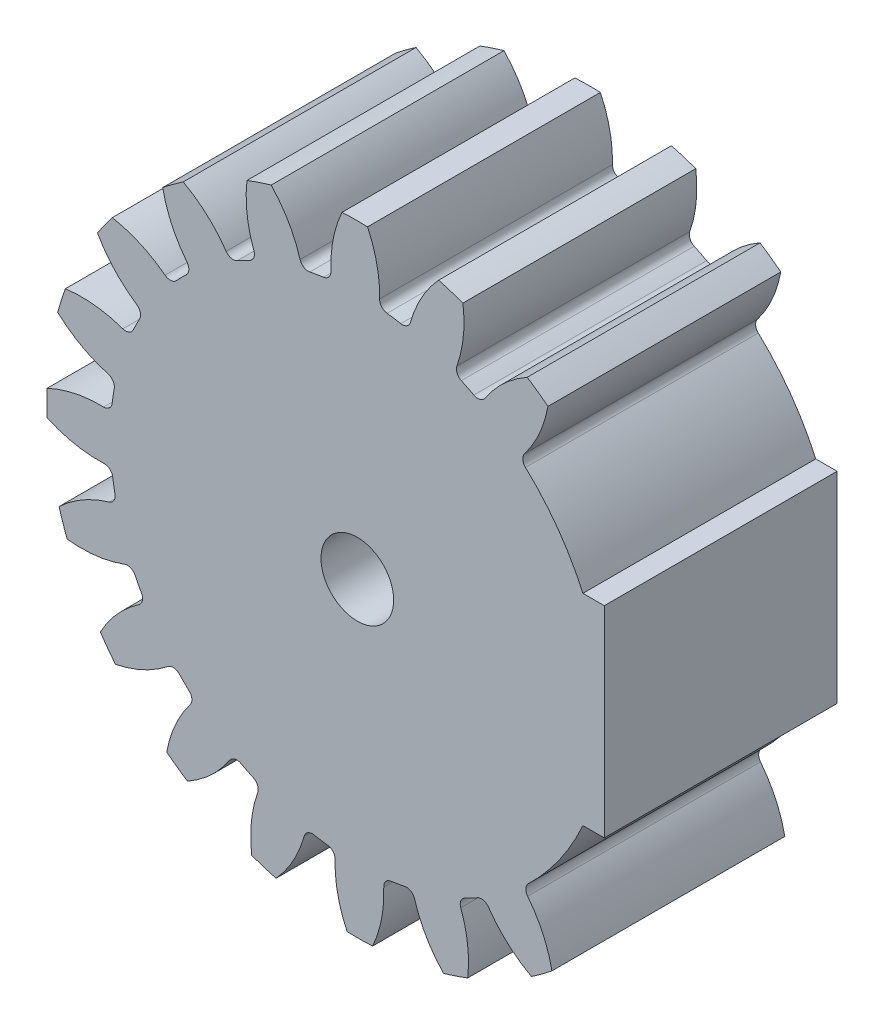
SolidWorks part; units mm, degrees
material "1023 Carbon Steel Sheet (SS)"
ref_plane "Front Plane" through (0, 0, 0) normal (0, 0, 1) x (1, 0, 0)
ref_plane "Top Plane" through (0, 0, 0) normal (0, 1, 0) x (1, 0, 0)
ref_plane "Right Plane" through (0, 0, 0) normal (1, 0, 0) x (0, 0, -1)
sketch "skBase" plane through (0, 0, 0) normal (0, 0, 1) x (1, 0, 0)
  circle A0 centre (0, 0) radius 20
  circle A1 centre (0, 0) radius 22
  circle A2 centre (0, 0) radius 17.5
  dimension "D1" = 40
  dimension "D3" = 4.5
extrude "Base" add sketch "skBase" along normal mid plane 16.5 contours A1
sketch "skToothProfile" plane through (0, 0, 0) normal (0, 0, 1) x (1, 0, 0)
  line L0 (0, 0) -> (0, 22) construction
  line L1 (-1.5692, 19.9383) -> (1.5692, 19.9383) construction
  line L2 (-1.0563, 17.4681) -> (0, 0) construction
  line L3 (0, 15.6271) -> (-2.6287, 22.8493) construction
  line L4 (0, 0) -> (3.4416, 21.7291) construction
  line L5 (1.5692, 19.9383) -> (4.6689, 19.4474) construction
  circle A0 centre (0, 0) radius 22 construction
  arc A1 (-1.0563, 17.4681) -> (-3.258, 22.7681) centre (-9.8105, 16.9387) ccw
  arc A2 (1.0563, 17.4681) -> (3.258, 22.7681) centre (9.8105, 16.9387) cw
  circle A3 centre (0, 0) radius 17.5 construction
  arc A4 (1.0563, 17.4681) -> (-1.0563, 17.4681) centre (0, 0) ccw
  circle A5 centre (0, 0) radius 20 construction
  circle A6 centre (0, 0) radius 22 construction
  circle A7 centre (0, 0) radius 23
  arc A8 (3.258, 22.7681) -> (-3.258, 22.7681) centre (0, 0) ccw
  dimension "D2" = 20
  dimension "D3" = 9
  dimension "D1" = 1
extrude "ToothProfile" cut sketch "skToothProfile" against normal through all and the other way through all
fillet "FilletToothProfile" radius 0.6 2 edges at (1.0563, 17.4681, 0) (-1.0563, 17.4681, 0)
pattern_circular "CirPatternTeeth" count 20 over 360 about axis through (0, 0, 0) along (0, 0, 1) of "ToothProfile", "FilletToothProfile"
sketch "skChaveta" plane through (0, 0, 8.25) normal (0, 0, 1) x (1, 0, 0)
  line L0 (0, 2.575) -> (0, 0) construction
  circle A0 centre (0, 0) radius 2.575
  dimension "D1" = 5.15
extrude "Chaveta" cut sketch "skChaveta" against normal through all
sketch "skRebaixo" plane through (0, 0, 8.25) normal (0, 0, 1) x (1, 0, 0)
  circle A0 centre (0, 0) radius 21.5
  circle A1 centre (0, 0) radius 7.5
  dimension "D1" = 43
  dimension "D2" = 15
sketch "Sketch4" plane through (0, 0, -8.25) normal (0, 0, -1) x (-1, 0, 0)
  circle A0 centre (0, 0) radius 17.5
  arc A5 (-2.5459, 21.8522) -> (-4.3314, 21.5694) centre (0, 0) ccw
  arc A6 (-2.5459, 21.8522) -> (-4.3314, 21.5694) centre (0, 0) ccw
  arc A7 (-18.0189, -1.107) -> (-21.8522, -2.5459) centre (-16.9387, -9.8105) ccw
  arc A8 (-18.0189, -1.107) -> (-21.8522, -2.5459) centre (-16.9387, -9.8105) ccw
  arc A9 (-21.5694, -4.3314) -> (-17.4791, -4.5153) centre (-19.1413, 4.096) ccw
  arc A10 (-21.5694, -4.3314) -> (-17.4791, -4.5153) centre (-19.1413, 4.096) ccw
  arc A127 (-19.996, -9.174) -> (-19.1752, -10.7848) centre (0, 0) ccw
  arc A128 (-19.996, -9.174) -> (-19.1752, -10.7848) centre (0, 0) ccw
  arc A129 (-16.1824, -14.904) -> (-14.904, -16.1824) centre (0, 0) ccw
  arc A130 (-16.1824, -14.904) -> (-14.904, -16.1824) centre (0, 0) ccw
  arc A131 (-10.7848, -19.1752) -> (-9.174, -19.996) centre (0, 0) ccw
  arc A132 (-10.7848, -19.1752) -> (-9.174, -19.996) centre (0, 0) ccw
  arc A133 (-4.3314, -21.5694) -> (-2.5459, -21.8522) centre (0, 0) ccw
  arc A134 (-4.3314, -21.5694) -> (-2.5459, -21.8522) centre (0, 0) ccw
  arc A135 (2.5459, -21.8522) -> (4.3314, -21.5694) centre (0, 0) ccw
  arc A136 (2.5459, -21.8522) -> (4.3314, -21.5694) centre (0, 0) ccw
  arc A137 (9.174, -19.996) -> (10.7848, -19.1752) centre (0, 0) ccw
  arc A138 (9.174, -19.996) -> (10.7848, -19.1752) centre (0, 0) ccw
  arc A139 (14.904, -16.1824) -> (16.1824, -14.904) centre (0, 0) ccw
  arc A140 (14.904, -16.1824) -> (16.1824, -14.904) centre (0, 0) ccw
  arc A141 (19.1752, -10.7848) -> (19.996, -9.174) centre (0, 0) ccw
  arc A142 (19.1752, -10.7848) -> (19.996, -9.174) centre (0, 0) ccw
  arc A143 (21.5694, -4.3314) -> (21.8522, -2.5459) centre (0, 0) ccw
  arc A144 (21.5694, -4.3314) -> (21.8522, -2.5459) centre (0, 0) ccw
  arc A145 (21.8522, 2.5459) -> (21.5694, 4.3314) centre (0, 0) ccw
  arc A146 (21.8522, 2.5459) -> (21.5694, 4.3314) centre (0, 0) ccw
  arc A147 (19.996, 9.174) -> (19.1752, 10.7848) centre (0, 0) ccw
  arc A148 (19.996, 9.174) -> (19.1752, 10.7848) centre (0, 0) ccw
  arc A149 (16.1824, 14.904) -> (14.904, 16.1824) centre (0, 0) ccw
  arc A150 (16.1824, 14.904) -> (14.904, 16.1824) centre (0, 0) ccw
  arc A151 (10.7848, 19.1752) -> (9.174, 19.996) centre (0, 0) ccw
  arc A152 (10.7848, 19.1752) -> (9.174, 19.996) centre (0, 0) ccw
  arc A153 (4.3314, 21.5694) -> (2.5459, 21.8522) centre (0, 0) ccw
  arc A154 (4.3314, 21.5694) -> (2.5459, 21.8522) centre (0, 0) ccw
  arc A155 (-9.174, 19.996) -> (-10.7848, 19.1752) centre (0, 0) ccw
  arc A156 (-9.174, 19.996) -> (-10.7848, 19.1752) centre (0, 0) ccw
  arc A157 (-14.904, 16.1824) -> (-16.1824, 14.904) centre (0, 0) ccw
  arc A158 (-14.904, 16.1824) -> (-16.1824, 14.904) centre (0, 0) ccw
  arc A159 (-19.1752, 10.7848) -> (-19.996, 9.174) centre (0, 0) ccw
  arc A160 (-19.1752, 10.7848) -> (-19.996, 9.174) centre (0, 0) ccw
  arc A161 (-21.5694, 4.3314) -> (-21.8522, 2.5459) centre (0, 0) ccw
  arc A162 (-21.5694, 4.3314) -> (-21.8522, 2.5459) centre (0, 0) ccw
  arc A163 (-4.3314, 21.5694) -> (-4.5153, 17.4791) centre (4.096, 19.1413) ccw
  arc A164 (-4.3314, 21.5694) -> (-4.5153, 17.4791) centre (4.096, 19.1413) ccw
  arc A165 (-4.9352, 16.7897) -> (-4.5153, 17.4791) centre (-5.1044, 17.3653) ccw
  arc A166 (-4.9352, 16.7897) -> (-4.5153, 17.4791) centre (-5.1044, 17.3653) ccw
  arc A167 (-4.9352, 16.7897) -> (-5.8761, 16.484) centre (0, 0) ccw
  arc A168 (-4.9352, 16.7897) -> (-5.8761, 16.484) centre (0, 0) ccw
  arc A169 (-6.621, 16.7949) -> (-5.8761, 16.484) centre (-6.0775, 17.0492) ccw
  arc A170 (-6.621, 16.7949) -> (-5.8761, 16.484) centre (-6.0775, 17.0492) ccw
  arc A171 (-6.621, 16.7949) -> (-9.174, 19.996) centre (-14.5647, 13.0781) ccw
  arc A172 (-6.621, 16.7949) -> (-9.174, 19.996) centre (-14.5647, 13.0781) ccw
  arc A173 (-10.7848, 19.1752) -> (-9.6956, 15.2283) centre (-2.0195, 19.4702) ccw
  arc A174 (-10.7848, 19.1752) -> (-9.6956, 15.2283) centre (-2.0195, 19.4702) ccw
  arc A175 (-9.882, 14.4429) -> (-9.6956, 15.2283) centre (-10.2208, 14.9381) ccw
  arc A176 (-9.882, 14.4429) -> (-9.6956, 15.2283) centre (-10.2208, 14.9381) ccw
  arc A177 (-9.882, 14.4429) -> (-10.6823, 13.8614) centre (0, 0) ccw
  arc A178 (-9.882, 14.4429) -> (-10.6823, 13.8614) centre (0, 0) ccw
  arc A179 (-11.4868, 13.9269) -> (-10.6823, 13.8614) centre (-11.0486, 14.3366) ccw
  arc A180 (-11.4868, 13.9269) -> (-10.6823, 13.8614) centre (-11.0486, 14.3366) ccw
  arc A181 (-11.4868, 13.9269) -> (-14.904, 16.1824) centre (-17.8932, 7.9372) ccw
  arc A182 (-11.4868, 13.9269) -> (-14.904, 16.1824) centre (-17.8932, 7.9372) ccw
  arc A183 (-16.1824, 14.904) -> (-13.9269, 11.4868) centre (-7.9372, 17.8932) ccw
  arc A184 (-16.1824, 14.904) -> (-13.9269, 11.4868) centre (-7.9372, 17.8932) ccw
  arc A185 (-13.8614, 10.6823) -> (-13.9269, 11.4868) centre (-14.3366, 11.0486) ccw
  arc A186 (-13.8614, 10.6823) -> (-13.9269, 11.4868) centre (-14.3366, 11.0486) ccw
  arc A187 (-13.8614, 10.6823) -> (-14.4429, 9.882) centre (0, 0) ccw
  arc A188 (-13.8614, 10.6823) -> (-14.4429, 9.882) centre (0, 0) ccw
  arc A189 (-15.2283, 9.6956) -> (-14.4429, 9.882) centre (-14.9381, 10.2208) ccw
  arc A190 (-15.2283, 9.6956) -> (-14.4429, 9.882) centre (-14.9381, 10.2208) ccw
  arc A191 (-15.2283, 9.6956) -> (-19.1752, 10.7848) centre (-19.4702, 2.0195) ccw
  arc A192 (-15.2283, 9.6956) -> (-19.1752, 10.7848) centre (-19.4702, 2.0195) ccw
  arc A193 (-19.996, 9.174) -> (-16.7949, 6.621) centre (-13.0781, 14.5647) ccw
  arc A194 (-19.996, 9.174) -> (-16.7949, 6.621) centre (-13.0781, 14.5647) ccw
  arc A195 (-16.484, 5.8761) -> (-16.7949, 6.621) centre (-17.0492, 6.0775) ccw
  arc A196 (-16.484, 5.8761) -> (-16.7949, 6.621) centre (-17.0492, 6.0775) ccw
  arc A197 (-16.484, 5.8761) -> (-16.7897, 4.9352) centre (0, 0) ccw
  arc A198 (-16.484, 5.8761) -> (-16.7897, 4.9352) centre (0, 0) ccw
  arc A199 (-17.4791, 4.5153) -> (-16.7897, 4.9352) centre (-17.3653, 5.1044) ccw
  arc A200 (-17.4791, 4.5153) -> (-16.7897, 4.9352) centre (-17.3653, 5.1044) ccw
  arc A201 (-17.4791, 4.5153) -> (-21.5694, 4.3314) centre (-19.1413, -4.096) ccw
  arc A202 (-17.4791, 4.5153) -> (-21.5694, 4.3314) centre (-19.1413, -4.096) ccw
  arc A203 (-21.8522, 2.5459) -> (-18.0189, 1.107) centre (-16.9387, 9.8105) ccw
  arc A204 (-21.8522, 2.5459) -> (-18.0189, 1.107) centre (-16.9387, 9.8105) ccw
  arc A205 (-17.493, 0.4946) -> (-18.0189, 1.107) centre (-18.0928, 0.5116) ccw
  arc A206 (-17.493, 0.4946) -> (-18.0189, 1.107) centre (-18.0928, 0.5116) ccw
  arc A207 (-17.493, 0.4946) -> (-17.493, -0.4946) centre (0, 0) ccw
  arc A208 (-17.493, 0.4946) -> (-17.493, -0.4946) centre (0, 0) ccw
  arc A209 (-18.0189, -1.107) -> (-17.493, -0.4946) centre (-18.0928, -0.5116) ccw
  arc A210 (-18.0189, -1.107) -> (-17.493, -0.4946) centre (-18.0928, -0.5116) ccw
  arc A211 (-16.7897, -4.9352) -> (-17.4791, -4.5153) centre (-17.3653, -5.1044) ccw
  arc A212 (-16.7897, -4.9352) -> (-17.4791, -4.5153) centre (-17.3653, -5.1044) ccw
  arc A213 (-16.7897, -4.9352) -> (-16.484, -5.8761) centre (0, 0) ccw
  arc A214 (-16.7897, -4.9352) -> (-16.484, -5.8761) centre (0, 0) ccw
  arc A215 (-16.7949, -6.621) -> (-16.484, -5.8761) centre (-17.0492, -6.0775) ccw
  arc A216 (-16.7949, -6.621) -> (-16.484, -5.8761) centre (-17.0492, -6.0775) ccw
  arc A217 (-16.7949, -6.621) -> (-19.996, -9.174) centre (-13.0781, -14.5647) ccw
  arc A218 (-16.7949, -6.621) -> (-19.996, -9.174) centre (-13.0781, -14.5647) ccw
  arc A219 (-19.1752, -10.7848) -> (-15.2283, -9.6956) centre (-19.4702, -2.0195) ccw
  arc A220 (-19.1752, -10.7848) -> (-15.2283, -9.6956) centre (-19.4702, -2.0195) ccw
  arc A221 (-14.4429, -9.882) -> (-15.2283, -9.6956) centre (-14.9381, -10.2208) ccw
  arc A222 (-14.4429, -9.882) -> (-15.2283, -9.6956) centre (-14.9381, -10.2208) ccw
  arc A223 (-14.4429, -9.882) -> (-13.8614, -10.6823) centre (0, 0) ccw
  arc A224 (-14.4429, -9.882) -> (-13.8614, -10.6823) centre (0, 0) ccw
  arc A225 (-13.9269, -11.4868) -> (-13.8614, -10.6823) centre (-14.3366, -11.0486) ccw
  arc A226 (-13.9269, -11.4868) -> (-13.8614, -10.6823) centre (-14.3366, -11.0486) ccw
  arc A227 (-13.9269, -11.4868) -> (-16.1824, -14.904) centre (-7.9372, -17.8932) ccw
  arc A228 (-13.9269, -11.4868) -> (-16.1824, -14.904) centre (-7.9372, -17.8932) ccw
  arc A229 (-14.904, -16.1824) -> (-11.4868, -13.9269) centre (-17.8932, -7.9372) ccw
  arc A230 (-14.904, -16.1824) -> (-11.4868, -13.9269) centre (-17.8932, -7.9372) ccw
  arc A231 (-10.6823, -13.8614) -> (-11.4868, -13.9269) centre (-11.0486, -14.3366) ccw
  arc A232 (-10.6823, -13.8614) -> (-11.4868, -13.9269) centre (-11.0486, -14.3366) ccw
  arc A233 (-10.6823, -13.8614) -> (-9.882, -14.4429) centre (0, 0) ccw
  arc A234 (-10.6823, -13.8614) -> (-9.882, -14.4429) centre (0, 0) ccw
  arc A235 (-9.6956, -15.2283) -> (-9.882, -14.4429) centre (-10.2208, -14.9381) ccw
  arc A236 (-9.6956, -15.2283) -> (-9.882, -14.4429) centre (-10.2208, -14.9381) ccw
  arc A237 (-9.6956, -15.2283) -> (-10.7848, -19.1752) centre (-2.0195, -19.4702) ccw
  arc A238 (-9.6956, -15.2283) -> (-10.7848, -19.1752) centre (-2.0195, -19.4702) ccw
  arc A239 (-9.174, -19.996) -> (-6.621, -16.7949) centre (-14.5647, -13.0781) ccw
  arc A240 (-9.174, -19.996) -> (-6.621, -16.7949) centre (-14.5647, -13.0781) ccw
  arc A241 (-5.8761, -16.484) -> (-6.621, -16.7949) centre (-6.0775, -17.0492) ccw
  arc A242 (-5.8761, -16.484) -> (-6.621, -16.7949) centre (-6.0775, -17.0492) ccw
  arc A243 (-5.8761, -16.484) -> (-4.9352, -16.7897) centre (0, 0) ccw
  arc A244 (-5.8761, -16.484) -> (-4.9352, -16.7897) centre (0, 0) ccw
  arc A245 (-4.5153, -17.4791) -> (-4.9352, -16.7897) centre (-5.1044, -17.3653) ccw
  arc A246 (-4.5153, -17.4791) -> (-4.9352, -16.7897) centre (-5.1044, -17.3653) ccw
  arc A247 (-4.5153, -17.4791) -> (-4.3314, -21.5694) centre (4.096, -19.1413) ccw
  arc A248 (-4.5153, -17.4791) -> (-4.3314, -21.5694) centre (4.096, -19.1413) ccw
  arc A249 (-2.5459, -21.8522) -> (-1.107, -18.0189) centre (-9.8105, -16.9387) ccw
  arc A250 (-2.5459, -21.8522) -> (-1.107, -18.0189) centre (-9.8105, -16.9387) ccw
  arc A251 (-0.4946, -17.493) -> (-1.107, -18.0189) centre (-0.5116, -18.0928) ccw
  arc A252 (-0.4946, -17.493) -> (-1.107, -18.0189) centre (-0.5116, -18.0928) ccw
  arc A253 (-0.4946, -17.493) -> (0.4946, -17.493) centre (0, 0) ccw
  arc A254 (-0.4946, -17.493) -> (0.4946, -17.493) centre (0, 0) ccw
  arc A255 (1.107, -18.0189) -> (0.4946, -17.493) centre (0.5116, -18.0928) ccw
  arc A256 (1.107, -18.0189) -> (0.4946, -17.493) centre (0.5116, -18.0928) ccw
  arc A257 (1.107, -18.0189) -> (2.5459, -21.8522) centre (9.8105, -16.9387) ccw
  arc A258 (1.107, -18.0189) -> (2.5459, -21.8522) centre (9.8105, -16.9387) ccw
  arc A259 (4.3314, -21.5694) -> (4.5153, -17.4791) centre (-4.096, -19.1413) ccw
  arc A260 (4.3314, -21.5694) -> (4.5153, -17.4791) centre (-4.096, -19.1413) ccw
  arc A261 (4.9352, -16.7897) -> (4.5153, -17.4791) centre (5.1044, -17.3653) ccw
  arc A262 (4.9352, -16.7897) -> (4.5153, -17.4791) centre (5.1044, -17.3653) ccw
  arc A263 (4.9352, -16.7897) -> (5.8761, -16.484) centre (0, 0) ccw
  arc A264 (4.9352, -16.7897) -> (5.8761, -16.484) centre (0, 0) ccw
  arc A265 (6.621, -16.7949) -> (5.8761, -16.484) centre (6.0775, -17.0492) ccw
  arc A266 (6.621, -16.7949) -> (5.8761, -16.484) centre (6.0775, -17.0492) ccw
  arc A267 (6.621, -16.7949) -> (9.174, -19.996) centre (14.5647, -13.0781) ccw
  arc A268 (6.621, -16.7949) -> (9.174, -19.996) centre (14.5647, -13.0781) ccw
  arc A269 (10.7848, -19.1752) -> (9.6956, -15.2283) centre (2.0195, -19.4702) ccw
  arc A270 (10.7848, -19.1752) -> (9.6956, -15.2283) centre (2.0195, -19.4702) ccw
  arc A271 (9.882, -14.4429) -> (9.6956, -15.2283) centre (10.2208, -14.9381) ccw
  arc A272 (9.882, -14.4429) -> (9.6956, -15.2283) centre (10.2208, -14.9381) ccw
  arc A273 (9.882, -14.4429) -> (10.6823, -13.8614) centre (0, 0) ccw
  arc A274 (9.882, -14.4429) -> (10.6823, -13.8614) centre (0, 0) ccw
  arc A275 (11.4868, -13.9269) -> (10.6823, -13.8614) centre (11.0486, -14.3366) ccw
  arc A276 (11.4868, -13.9269) -> (10.6823, -13.8614) centre (11.0486, -14.3366) ccw
  arc A277 (11.4868, -13.9269) -> (14.904, -16.1824) centre (17.8932, -7.9372) ccw
  arc A278 (11.4868, -13.9269) -> (14.904, -16.1824) centre (17.8932, -7.9372) ccw
  arc A279 (16.1824, -14.904) -> (13.9269, -11.4868) centre (7.9372, -17.8932) ccw
  arc A280 (16.1824, -14.904) -> (13.9269, -11.4868) centre (7.9372, -17.8932) ccw
  arc A281 (13.8614, -10.6823) -> (13.9269, -11.4868) centre (14.3366, -11.0486) ccw
  arc A282 (13.8614, -10.6823) -> (13.9269, -11.4868) centre (14.3366, -11.0486) ccw
  arc A283 (13.8614, -10.6823) -> (14.4429, -9.882) centre (0, 0) ccw
  arc A284 (13.8614, -10.6823) -> (14.4429, -9.882) centre (0, 0) ccw
  arc A285 (15.2283, -9.6956) -> (14.4429, -9.882) centre (14.9381, -10.2208) ccw
  arc A286 (15.2283, -9.6956) -> (14.4429, -9.882) centre (14.9381, -10.2208) ccw
  arc A287 (15.2283, -9.6956) -> (19.1752, -10.7848) centre (19.4702, -2.0195) ccw
  arc A288 (15.2283, -9.6956) -> (19.1752, -10.7848) centre (19.4702, -2.0195) ccw
  arc A289 (19.996, -9.174) -> (16.7949, -6.621) centre (13.0781, -14.5647) ccw
  arc A290 (19.996, -9.174) -> (16.7949, -6.621) centre (13.0781, -14.5647) ccw
  arc A291 (16.484, -5.8761) -> (16.7949, -6.621) centre (17.0492, -6.0775) ccw
  arc A292 (16.484, -5.8761) -> (16.7949, -6.621) centre (17.0492, -6.0775) ccw
  arc A293 (16.484, -5.8761) -> (16.7897, -4.9352) centre (0, 0) ccw
  arc A294 (16.484, -5.8761) -> (16.7897, -4.9352) centre (0, 0) ccw
  arc A295 (17.4791, -4.5153) -> (16.7897, -4.9352) centre (17.3653, -5.1044) ccw
  arc A296 (17.4791, -4.5153) -> (16.7897, -4.9352) centre (17.3653, -5.1044) ccw
  arc A297 (17.4791, -4.5153) -> (21.5694, -4.3314) centre (19.1413, 4.096) ccw
  arc A298 (17.4791, -4.5153) -> (21.5694, -4.3314) centre (19.1413, 4.096) ccw
  arc A299 (21.8522, -2.5459) -> (18.0189, -1.107) centre (16.9387, -9.8105) ccw
  arc A300 (21.8522, -2.5459) -> (18.0189, -1.107) centre (16.9387, -9.8105) ccw
  arc A301 (17.493, -0.4946) -> (18.0189, -1.107) centre (18.0928, -0.5116) ccw
  arc A302 (17.493, -0.4946) -> (18.0189, -1.107) centre (18.0928, -0.5116) ccw
  arc A303 (17.493, -0.4946) -> (17.493, 0.4946) centre (0, 0) ccw
  arc A304 (17.493, -0.4946) -> (17.493, 0.4946) centre (0, 0) ccw
  arc A305 (18.0189, 1.107) -> (17.493, 0.4946) centre (18.0928, 0.5116) ccw
  arc A306 (18.0189, 1.107) -> (17.493, 0.4946) centre (18.0928, 0.5116) ccw
  arc A307 (18.0189, 1.107) -> (21.8522, 2.5459) centre (16.9387, 9.8105) ccw
  arc A308 (18.0189, 1.107) -> (21.8522, 2.5459) centre (16.9387, 9.8105) ccw
  arc A309 (21.5694, 4.3314) -> (17.4791, 4.5153) centre (19.1413, -4.096) ccw
  arc A310 (21.5694, 4.3314) -> (17.4791, 4.5153) centre (19.1413, -4.096) ccw
  arc A311 (-21.8522, -2.5459) -> (-21.5694, -4.3314) centre (0, 0) ccw
  arc A312 (-21.8522, -2.5459) -> (-21.5694, -4.3314) centre (0, 0) ccw
  arc A313 (16.7897, 4.9352) -> (17.4791, 4.5153) centre (17.3653, 5.1044) ccw
  arc A314 (16.7897, 4.9352) -> (17.4791, 4.5153) centre (17.3653, 5.1044) ccw
  arc A315 (16.7897, 4.9352) -> (16.484, 5.8761) centre (0, 0) ccw
  arc A316 (16.7897, 4.9352) -> (16.484, 5.8761) centre (0, 0) ccw
  arc A317 (16.7949, 6.621) -> (16.484, 5.8761) centre (17.0492, 6.0775) ccw
  arc A318 (16.7949, 6.621) -> (16.484, 5.8761) centre (17.0492, 6.0775) ccw
  arc A319 (16.7949, 6.621) -> (19.996, 9.174) centre (13.0781, 14.5647) ccw
  arc A320 (16.7949, 6.621) -> (19.996, 9.174) centre (13.0781, 14.5647) ccw
  arc A321 (19.1752, 10.7848) -> (15.2283, 9.6956) centre (19.4702, 2.0195) ccw
  arc A322 (19.1752, 10.7848) -> (15.2283, 9.6956) centre (19.4702, 2.0195) ccw
  arc A323 (14.4429, 9.882) -> (15.2283, 9.6956) centre (14.9381, 10.2208) ccw
  arc A324 (14.4429, 9.882) -> (15.2283, 9.6956) centre (14.9381, 10.2208) ccw
  arc A325 (14.4429, 9.882) -> (13.8614, 10.6823) centre (0, 0) ccw
  arc A326 (14.4429, 9.882) -> (13.8614, 10.6823) centre (0, 0) ccw
  arc A327 (13.9269, 11.4868) -> (13.8614, 10.6823) centre (14.3366, 11.0486) ccw
  arc A328 (13.9269, 11.4868) -> (13.8614, 10.6823) centre (14.3366, 11.0486) ccw
  arc A329 (13.9269, 11.4868) -> (16.1824, 14.904) centre (7.9372, 17.8932) ccw
  arc A330 (13.9269, 11.4868) -> (16.1824, 14.904) centre (7.9372, 17.8932) ccw
  arc A331 (14.904, 16.1824) -> (11.4868, 13.9269) centre (17.8932, 7.9372) ccw
  arc A332 (14.904, 16.1824) -> (11.4868, 13.9269) centre (17.8932, 7.9372) ccw
  arc A333 (10.6823, 13.8614) -> (11.4868, 13.9269) centre (11.0486, 14.3366) ccw
  arc A334 (10.6823, 13.8614) -> (11.4868, 13.9269) centre (11.0486, 14.3366) ccw
  arc A335 (10.6823, 13.8614) -> (9.882, 14.4429) centre (0, 0) ccw
  arc A336 (10.6823, 13.8614) -> (9.882, 14.4429) centre (0, 0) ccw
  arc A337 (9.6956, 15.2283) -> (9.882, 14.4429) centre (10.2208, 14.9381) ccw
  arc A338 (9.6956, 15.2283) -> (9.882, 14.4429) centre (10.2208, 14.9381) ccw
  arc A339 (9.6956, 15.2283) -> (10.7848, 19.1752) centre (2.0195, 19.4702) ccw
  arc A340 (9.6956, 15.2283) -> (10.7848, 19.1752) centre (2.0195, 19.4702) ccw
  arc A341 (9.174, 19.996) -> (6.621, 16.7949) centre (14.5647, 13.0781) ccw
  arc A342 (9.174, 19.996) -> (6.621, 16.7949) centre (14.5647, 13.0781) ccw
  arc A343 (5.8761, 16.484) -> (6.621, 16.7949) centre (6.0775, 17.0492) ccw
  arc A344 (5.8761, 16.484) -> (6.621, 16.7949) centre (6.0775, 17.0492) ccw
  arc A345 (5.8761, 16.484) -> (4.9352, 16.7897) centre (0, 0) ccw
  arc A346 (5.8761, 16.484) -> (4.9352, 16.7897) centre (0, 0) ccw
  arc A347 (4.5153, 17.4791) -> (4.9352, 16.7897) centre (5.1044, 17.3653) ccw
  arc A348 (4.5153, 17.4791) -> (4.9352, 16.7897) centre (5.1044, 17.3653) ccw
  arc A349 (4.5153, 17.4791) -> (4.3314, 21.5694) centre (-4.096, 19.1413) ccw
  arc A350 (4.5153, 17.4791) -> (4.3314, 21.5694) centre (-4.096, 19.1413) ccw
  arc A351 (2.5459, 21.8522) -> (1.107, 18.0189) centre (9.8105, 16.9387) ccw
  arc A352 (2.5459, 21.8522) -> (1.107, 18.0189) centre (9.8105, 16.9387) ccw
  arc A353 (0.4946, 17.493) -> (1.107, 18.0189) centre (0.5116, 18.0928) ccw
  arc A354 (0.4946, 17.493) -> (1.107, 18.0189) centre (0.5116, 18.0928) ccw
  arc A355 (0.4946, 17.493) -> (-0.4946, 17.493) centre (0, 0) ccw
  arc A356 (0.4946, 17.493) -> (-0.4946, 17.493) centre (0, 0) ccw
  arc A357 (-1.107, 18.0189) -> (-0.4946, 17.493) centre (-0.5116, 18.0928) ccw
  arc A358 (-1.107, 18.0189) -> (-0.4946, 17.493) centre (-0.5116, 18.0928) ccw
  arc A359 (-1.107, 18.0189) -> (-2.5459, 21.8522) centre (-9.8105, 16.9387) ccw
  arc A360 (-1.107, 18.0189) -> (-2.5459, 21.8522) centre (-9.8105, 16.9387) ccw
  dimension "D1" = 0
sketch "Sketch6" plane through (0, 0, -8.25) normal (0, 0, -1) x (-1, 0, 0)
  circle A0 centre (0, 0) radius 20 construction
  dimension "D1" = 40
move or copy body "Body-Move/Copy1" bodies to move or copy 104 copy no rotation origin (0, 0, 0) rotation axis (0, 0, 1) rotation angle 9.47
sketch "Sketch7" plane through (0, 0, -8.25) normal (0, 0, -1) x (-1, 0, 0)
  circle A0 centre (0, 0) radius 17.5
  arc A120 (1.0842, 21.9733) -> (-0.7236, 21.9881) centre (0, 0) ccw
  arc A121 (-0.7236, 21.9881) -> (-1.5779, 17.9838) centre (7.1895, 18.2065) ccw
  arc A122 (-2.1055, 17.3729) -> (-1.5779, 17.9838) centre (-2.1777, 17.9685) ccw
  arc A123 (-2.1055, 17.3729) -> (-3.0839, 17.2261) centre (0, 0) ccw
  arc A124 (-3.7675, 17.6554) -> (-3.0839, 17.2261) centre (-3.1896, 17.8167) ccw
  arc A125 (-3.7675, 17.6554) -> (-5.759, 21.2329) centre (-12.2145, 15.2962) ccw
  arc A126 (-5.759, 21.2329) -> (-7.4829, 20.6883) centre (0, 0) ccw
  arc A127 (-7.4829, 20.6883) -> (-7.058, 16.616) centre (1.2115, 19.5371) ccw
  arc A128 (-7.371, 15.8719) -> (-7.058, 16.616) centre (-7.6237, 16.4161) ccw
  arc A129 (-7.371, 15.8719) -> (-8.2561, 15.4301) centre (0, 0) ccw
  arc A130 (-9.0389, 15.627) -> (-8.2561, 15.4301) centre (-8.5392, 15.9591) ccw
  arc A131 (-9.0389, 15.627) -> (-12.0384, 18.414) centre (-16.3435, 10.7731) ccw
  arc A132 (-12.0384, 18.414) -> (-13.5097, 17.3634) centre (0, 0) ccw
  arc A133 (-13.5097, 17.3634) -> (-11.8471, 13.6217) centre (-4.8851, 18.9553) ccw
  arc A134 (-11.9149, 12.8174) -> (-11.8471, 13.6217) centre (-12.3234, 13.2568) ccw
  arc A135 (-11.9149, 12.8174) -> (-12.6202, 12.1236) centre (0, 0) ccw
  arc A136 (-13.4255, 12.069) -> (-12.6202, 12.1236) centre (-13.0529, 12.5393) ccw
  arc A137 (-13.4255, 12.069) -> (-17.1395, 13.7927) centre (-18.8726, 5.1954) ccw
  arc A138 (-17.1395, 13.7927) -> (-18.2141, 12.3389) centre (0, 0) ccw
  arc A139 (-18.2141, 12.3389) -> (-15.4766, 9.294) centre (-10.5035, 16.518) ccw
  arc A140 (-15.2925, 8.5081) -> (-15.4766, 9.294) centre (-15.8169, 8.7998) ccw
  arc A141 (-15.2925, 8.5081) -> (-15.7489, 7.6304) centre (0, 0) ccw
  arc A142 (-16.4979, 7.3296) -> (-15.7489, 7.6304) centre (-16.2888, 7.892) ccw
  arc A143 (-16.4979, 7.3296) -> (-20.5628, 7.8212) centre (-19.5544, -0.8908) ccw
  arc A144 (-20.5628, 7.8212) -> (-21.1355, 6.1065) centre (0, 0) ccw
  arc A145 (-21.1355, 6.1065) -> (-17.5912, 4.0566) centre (-15.0938, 12.4638) ccw
  arc A146 (-17.1732, 3.3661) -> (-17.5912, 4.0566) centre (-17.762, 3.4815) ccw
  arc A147 (-17.1732, 3.3661) -> (-17.336, 2.3902) centre (0, 0) ccw
  arc A148 (-17.9555, 1.8727) -> (-17.336, 2.3902) centre (-17.9304, 2.4722) ccw
  arc A149 (-17.9555, 1.8727) -> (-21.9733, 1.0842) centre (-18.322, -6.8899) ccw
  arc A150 (-21.9733, 1.0842) -> (-21.9881, -0.7236) centre (0, 0) ccw
  arc A151 (-21.9881, -0.7236) -> (-17.9838, -1.5779) centre (-18.2065, 7.1895) ccw
  arc A152 (-17.3729, -2.1055) -> (-17.9838, -1.5779) centre (-17.9685, -2.1777) ccw
  arc A153 (-17.3729, -2.1055) -> (-17.2261, -3.0839) centre (0, 0) ccw
  arc A154 (-17.6554, -3.7675) -> (-17.2261, -3.0839) centre (-17.8167, -3.1896) ccw
  arc A155 (-17.6554, -3.7675) -> (-21.2329, -5.759) centre (-15.2962, -12.2145) ccw
  arc A156 (-21.2329, -5.759) -> (-20.6883, -7.4829) centre (0, 0) ccw
  arc A157 (-20.6883, -7.4829) -> (-16.616, -7.058) centre (-19.5371, 1.2115) ccw
  arc A158 (-15.8719, -7.371) -> (-16.616, -7.058) centre (-16.4161, -7.6237) ccw
  arc A159 (-15.8719, -7.371) -> (-15.4301, -8.2561) centre (0, 0) ccw
  arc A160 (-15.627, -9.0389) -> (-15.4301, -8.2561) centre (-15.9591, -8.5392) ccw
  arc A161 (-15.627, -9.0389) -> (-18.414, -12.0384) centre (-10.7731, -16.3435) ccw
  arc A162 (-18.414, -12.0384) -> (-17.3634, -13.5097) centre (0, 0) ccw
  arc A163 (-17.3634, -13.5097) -> (-13.6217, -11.8471) centre (-18.9553, -4.8851) ccw
  arc A164 (-12.8174, -11.9149) -> (-13.6217, -11.8471) centre (-13.2568, -12.3234) ccw
  arc A165 (-12.8174, -11.9149) -> (-12.1236, -12.6202) centre (0, 0) ccw
  arc A166 (-12.069, -13.4255) -> (-12.1236, -12.6202) centre (-12.5393, -13.0529) ccw
  arc A167 (-12.069, -13.4255) -> (-13.7927, -17.1395) centre (-5.1954, -18.8726) ccw
  arc A168 (-13.7927, -17.1395) -> (-12.3389, -18.2141) centre (0, 0) ccw
  arc A169 (-12.3389, -18.2141) -> (-9.294, -15.4766) centre (-16.518, -10.5035) ccw
  arc A170 (-8.5081, -15.2925) -> (-9.294, -15.4766) centre (-8.7998, -15.8169) ccw
  arc A171 (-8.5081, -15.2925) -> (-7.6304, -15.7489) centre (0, 0) ccw
  arc A172 (-7.3296, -16.4979) -> (-7.6304, -15.7489) centre (-7.892, -16.2888) ccw
  arc A173 (-7.3296, -16.4979) -> (-7.8212, -20.5628) centre (0.8908, -19.5544) ccw
  arc A174 (-7.8212, -20.5628) -> (-6.1065, -21.1355) centre (0, 0) ccw
  arc A175 (-6.1065, -21.1355) -> (-4.0566, -17.5912) centre (-12.4638, -15.0938) ccw
  arc A176 (-3.3661, -17.1732) -> (-4.0566, -17.5912) centre (-3.4815, -17.762) ccw
  arc A177 (-3.3661, -17.1732) -> (-2.3902, -17.336) centre (0, 0) ccw
  arc A178 (-1.8727, -17.9555) -> (-2.3902, -17.336) centre (-2.4722, -17.9304) ccw
  arc A179 (-1.8727, -17.9555) -> (-1.0842, -21.9733) centre (6.8899, -18.322) ccw
  arc A180 (-1.0842, -21.9733) -> (0.7236, -21.9881) centre (0, 0) ccw
  arc A181 (0.7236, -21.9881) -> (1.5779, -17.9838) centre (-7.1895, -18.2065) ccw
  arc A182 (2.1055, -17.3729) -> (1.5779, -17.9838) centre (2.1777, -17.9685) ccw
  arc A183 (2.1055, -17.3729) -> (3.0839, -17.2261) centre (0, 0) ccw
  arc A184 (3.7675, -17.6554) -> (3.0839, -17.2261) centre (3.1896, -17.8167) ccw
  arc A185 (3.7675, -17.6554) -> (5.759, -21.2329) centre (12.2145, -15.2962) ccw
  arc A186 (5.759, -21.2329) -> (7.4829, -20.6883) centre (0, 0) ccw
  arc A187 (7.4829, -20.6883) -> (7.058, -16.616) centre (-1.2115, -19.5371) ccw
  arc A188 (7.371, -15.8719) -> (7.058, -16.616) centre (7.6237, -16.4161) ccw
  arc A189 (7.371, -15.8719) -> (8.2561, -15.4301) centre (0, 0) ccw
  arc A190 (9.0389, -15.627) -> (8.2561, -15.4301) centre (8.5392, -15.9591) ccw
  arc A191 (9.0389, -15.627) -> (12.0384, -18.414) centre (16.3435, -10.7731) ccw
  arc A192 (12.0384, -18.414) -> (13.5097, -17.3634) centre (0, 0) ccw
  arc A193 (13.5097, -17.3634) -> (11.8471, -13.6217) centre (4.8851, -18.9553) ccw
  arc A194 (11.9149, -12.8174) -> (11.8471, -13.6217) centre (12.3234, -13.2568) ccw
  arc A195 (11.9149, -12.8174) -> (12.6202, -12.1236) centre (0, 0) ccw
  arc A196 (13.4255, -12.069) -> (12.6202, -12.1236) centre (13.0529, -12.5393) ccw
  arc A197 (13.4255, -12.069) -> (17.1395, -13.7927) centre (18.8726, -5.1954) ccw
  arc A198 (17.1395, -13.7927) -> (18.2141, -12.3389) centre (0, 0) ccw
  arc A199 (18.2141, -12.3389) -> (15.4766, -9.294) centre (10.5035, -16.518) ccw
  arc A200 (15.2925, -8.5081) -> (15.4766, -9.294) centre (15.8169, -8.7998) ccw
  arc A201 (15.2925, -8.5081) -> (15.7489, -7.6304) centre (0, 0) ccw
  arc A202 (16.4979, -7.3296) -> (15.7489, -7.6304) centre (16.2888, -7.892) ccw
  arc A203 (16.4979, -7.3296) -> (20.5628, -7.8212) centre (19.5544, 0.8908) ccw
  arc A204 (20.5628, -7.8212) -> (21.1355, -6.1065) centre (0, 0) ccw
  arc A205 (21.1355, -6.1065) -> (17.5912, -4.0566) centre (15.0938, -12.4638) ccw
  arc A206 (17.1732, -3.3661) -> (17.5912, -4.0566) centre (17.762, -3.4815) ccw
  arc A207 (17.1732, -3.3661) -> (17.336, -2.3902) centre (0, 0) ccw
  arc A208 (17.9555, -1.8727) -> (17.336, -2.3902) centre (17.9304, -2.4722) ccw
  arc A209 (17.9555, -1.8727) -> (21.9733, -1.0842) centre (18.322, 6.8899) ccw
  arc A210 (21.9733, -1.0842) -> (21.9881, 0.7236) centre (0, 0) ccw
  arc A211 (21.9881, 0.7236) -> (17.9838, 1.5779) centre (18.2065, -7.1895) ccw
  arc A212 (17.3729, 2.1055) -> (17.9838, 1.5779) centre (17.9685, 2.1777) ccw
  arc A213 (17.3729, 2.1055) -> (17.2261, 3.0839) centre (0, 0) ccw
  arc A214 (17.6554, 3.7675) -> (17.2261, 3.0839) centre (17.8167, 3.1896) ccw
  arc A215 (17.6554, 3.7675) -> (21.2329, 5.759) centre (15.2962, 12.2145) ccw
  arc A216 (21.2329, 5.759) -> (20.6883, 7.4829) centre (0, 0) ccw
  arc A217 (20.6883, 7.4829) -> (16.616, 7.058) centre (19.5371, -1.2115) ccw
  arc A218 (15.8719, 7.371) -> (16.616, 7.058) centre (16.4161, 7.6237) ccw
  arc A219 (15.8719, 7.371) -> (15.4301, 8.2561) centre (0, 0) ccw
  arc A220 (15.627, 9.0389) -> (15.4301, 8.2561) centre (15.9591, 8.5392) ccw
  arc A221 (15.627, 9.0389) -> (18.414, 12.0384) centre (10.7731, 16.3435) ccw
  arc A222 (18.414, 12.0384) -> (17.3634, 13.5097) centre (0, 0) ccw
  arc A223 (17.3634, 13.5097) -> (13.6217, 11.8471) centre (18.9553, 4.8851) ccw
  arc A224 (12.8174, 11.9149) -> (13.6217, 11.8471) centre (13.2568, 12.3234) ccw
  arc A225 (12.8174, 11.9149) -> (12.1236, 12.6202) centre (0, 0) ccw
  arc A226 (12.069, 13.4255) -> (12.1236, 12.6202) centre (12.5393, 13.0529) ccw
  arc A227 (12.069, 13.4255) -> (13.7927, 17.1395) centre (5.1954, 18.8726) ccw
  arc A228 (13.7927, 17.1395) -> (12.3389, 18.2141) centre (0, 0) ccw
  arc A229 (12.3389, 18.2141) -> (9.294, 15.4766) centre (16.518, 10.5035) ccw
  arc A230 (8.5081, 15.2925) -> (9.294, 15.4766) centre (8.7998, 15.8169) ccw
  arc A231 (8.5081, 15.2925) -> (7.6304, 15.7489) centre (0, 0) ccw
  arc A232 (7.3296, 16.4979) -> (7.6304, 15.7489) centre (7.892, 16.2888) ccw
  arc A233 (7.3296, 16.4979) -> (7.8212, 20.5628) centre (-0.8908, 19.5544) ccw
  arc A234 (7.8212, 20.5628) -> (6.1065, 21.1355) centre (0, 0) ccw
  arc A235 (6.1065, 21.1355) -> (4.0566, 17.5912) centre (12.4638, 15.0938) ccw
  arc A236 (3.3661, 17.1732) -> (4.0566, 17.5912) centre (3.4815, 17.762) ccw
  arc A237 (3.3661, 17.1732) -> (2.3902, 17.336) centre (0, 0) ccw
  arc A238 (1.8727, 17.9555) -> (2.3902, 17.336) centre (2.4722, 17.9304) ccw
  arc A239 (1.8727, 17.9555) -> (1.0842, 21.9733) centre (-6.8899, 18.322) ccw
  arc A240 (1.0842, 21.9733) -> (-0.7236, 21.9881) centre (0, 0) ccw
  arc A241 (-0.7236, 21.9881) -> (-1.5779, 17.9838) centre (7.1895, 18.2065) ccw
  arc A242 (-2.1055, 17.3729) -> (-1.5779, 17.9838) centre (-2.1777, 17.9685) ccw
  arc A243 (-2.1055, 17.3729) -> (-3.0839, 17.2261) centre (0, 0) ccw
  arc A244 (-3.7675, 17.6554) -> (-3.0839, 17.2261) centre (-3.1896, 17.8167) ccw
  arc A245 (-3.7675, 17.6554) -> (-5.759, 21.2329) centre (-12.2145, 15.2962) ccw
  arc A246 (-5.759, 21.2329) -> (-7.4829, 20.6883) centre (0, 0) ccw
  arc A247 (-7.4829, 20.6883) -> (-7.058, 16.616) centre (1.2115, 19.5371) ccw
  arc A248 (-7.371, 15.8719) -> (-7.058, 16.616) centre (-7.6237, 16.4161) ccw
  arc A249 (-7.371, 15.8719) -> (-8.2561, 15.4301) centre (0, 0) ccw
  arc A250 (-9.0389, 15.627) -> (-8.2561, 15.4301) centre (-8.5392, 15.9591) ccw
  arc A251 (-9.0389, 15.627) -> (-12.0384, 18.414) centre (-16.3435, 10.7731) ccw
  arc A252 (-12.0384, 18.414) -> (-13.5097, 17.3634) centre (0, 0) ccw
  arc A253 (-13.5097, 17.3634) -> (-11.8471, 13.6217) centre (-4.8851, 18.9553) ccw
  arc A254 (-11.9149, 12.8174) -> (-11.8471, 13.6217) centre (-12.3234, 13.2568) ccw
  arc A255 (-11.9149, 12.8174) -> (-12.6202, 12.1236) centre (0, 0) ccw
  arc A256 (-13.4255, 12.069) -> (-12.6202, 12.1236) centre (-13.0529, 12.5393) ccw
  arc A257 (-13.4255, 12.069) -> (-17.1395, 13.7927) centre (-18.8726, 5.1954) ccw
  arc A258 (-17.1395, 13.7927) -> (-18.2141, 12.3389) centre (0, 0) ccw
  arc A259 (-18.2141, 12.3389) -> (-15.4766, 9.294) centre (-10.5035, 16.518) ccw
  arc A260 (-15.2925, 8.5081) -> (-15.4766, 9.294) centre (-15.8169, 8.7998) ccw
  arc A261 (-15.2925, 8.5081) -> (-15.7489, 7.6304) centre (0, 0) ccw
  arc A262 (-16.4979, 7.3296) -> (-15.7489, 7.6304) centre (-16.2888, 7.892) ccw
  arc A263 (-16.4979, 7.3296) -> (-20.5628, 7.8212) centre (-19.5544, -0.8908) ccw
  arc A264 (-20.5628, 7.8212) -> (-21.1355, 6.1065) centre (0, 0) ccw
  arc A265 (-21.1355, 6.1065) -> (-17.5912, 4.0566) centre (-15.0938, 12.4638) ccw
  arc A266 (-17.1732, 3.3661) -> (-17.5912, 4.0566) centre (-17.762, 3.4815) ccw
  arc A267 (-17.1732, 3.3661) -> (-17.336, 2.3902) centre (0, 0) ccw
  arc A268 (-17.9555, 1.8727) -> (-17.336, 2.3902) centre (-17.9304, 2.4722) ccw
  arc A269 (-17.9555, 1.8727) -> (-21.9733, 1.0842) centre (-18.322, -6.8899) ccw
  arc A270 (-21.9733, 1.0842) -> (-21.9881, -0.7236) centre (0, 0) ccw
  arc A271 (-21.9881, -0.7236) -> (-17.9838, -1.5779) centre (-18.2065, 7.1895) ccw
  arc A272 (-17.3729, -2.1055) -> (-17.9838, -1.5779) centre (-17.9685, -2.1777) ccw
  arc A273 (-17.3729, -2.1055) -> (-17.2261, -3.0839) centre (0, 0) ccw
  arc A274 (-17.6554, -3.7675) -> (-17.2261, -3.0839) centre (-17.8167, -3.1896) ccw
  arc A275 (-17.6554, -3.7675) -> (-21.2329, -5.759) centre (-15.2962, -12.2145) ccw
  arc A276 (-21.2329, -5.759) -> (-20.6883, -7.4829) centre (0, 0) ccw
  arc A277 (-20.6883, -7.4829) -> (-16.616, -7.058) centre (-19.5371, 1.2115) ccw
  arc A278 (-15.8719, -7.371) -> (-16.616, -7.058) centre (-16.4161, -7.6237) ccw
  arc A279 (-15.8719, -7.371) -> (-15.4301, -8.2561) centre (0, 0) ccw
  arc A280 (-15.627, -9.0389) -> (-15.4301, -8.2561) centre (-15.9591, -8.5392) ccw
  arc A281 (-15.627, -9.0389) -> (-18.414, -12.0384) centre (-10.7731, -16.3435) ccw
  arc A282 (-18.414, -12.0384) -> (-17.3634, -13.5097) centre (0, 0) ccw
  arc A283 (-17.3634, -13.5097) -> (-13.6217, -11.8471) centre (-18.9553, -4.8851) ccw
  arc A284 (-12.8174, -11.9149) -> (-13.6217, -11.8471) centre (-13.2568, -12.3234) ccw
  arc A285 (-12.8174, -11.9149) -> (-12.1236, -12.6202) centre (0, 0) ccw
  arc A286 (-12.069, -13.4255) -> (-12.1236, -12.6202) centre (-12.5393, -13.0529) ccw
  arc A287 (-12.069, -13.4255) -> (-13.7927, -17.1395) centre (-5.1954, -18.8726) ccw
  arc A288 (-13.7927, -17.1395) -> (-12.3389, -18.2141) centre (0, 0) ccw
  arc A289 (-12.3389, -18.2141) -> (-9.294, -15.4766) centre (-16.518, -10.5035) ccw
  arc A290 (-8.5081, -15.2925) -> (-9.294, -15.4766) centre (-8.7998, -15.8169) ccw
  arc A291 (-8.5081, -15.2925) -> (-7.6304, -15.7489) centre (0, 0) ccw
  arc A292 (-7.3296, -16.4979) -> (-7.6304, -15.7489) centre (-7.892, -16.2888) ccw
  arc A293 (-7.3296, -16.4979) -> (-7.8212, -20.5628) centre (0.8908, -19.5544) ccw
  arc A294 (-7.8212, -20.5628) -> (-6.1065, -21.1355) centre (0, 0) ccw
  arc A295 (-6.1065, -21.1355) -> (-4.0566, -17.5912) centre (-12.4638, -15.0938) ccw
  arc A296 (-3.3661, -17.1732) -> (-4.0566, -17.5912) centre (-3.4815, -17.762) ccw
  arc A297 (-3.3661, -17.1732) -> (-2.3902, -17.336) centre (0, 0) ccw
  arc A298 (-1.8727, -17.9555) -> (-2.3902, -17.336) centre (-2.4722, -17.9304) ccw
  arc A299 (-1.8727, -17.9555) -> (-1.0842, -21.9733) centre (6.8899, -18.322) ccw
  arc A300 (-1.0842, -21.9733) -> (0.7236, -21.9881) centre (0, 0) ccw
  arc A301 (0.7236, -21.9881) -> (1.5779, -17.9838) centre (-7.1895, -18.2065) ccw
  arc A302 (2.1055, -17.3729) -> (1.5779, -17.9838) centre (2.1777, -17.9685) ccw
  arc A303 (2.1055, -17.3729) -> (3.0839, -17.2261) centre (0, 0) ccw
  arc A304 (3.7675, -17.6554) -> (3.0839, -17.2261) centre (3.1896, -17.8167) ccw
  arc A305 (3.7675, -17.6554) -> (5.759, -21.2329) centre (12.2145, -15.2962) ccw
  arc A306 (5.759, -21.2329) -> (7.4829, -20.6883) centre (0, 0) ccw
  arc A307 (7.4829, -20.6883) -> (7.058, -16.616) centre (-1.2115, -19.5371) ccw
  arc A308 (7.371, -15.8719) -> (7.058, -16.616) centre (7.6237, -16.4161) ccw
  arc A309 (7.371, -15.8719) -> (8.2561, -15.4301) centre (0, 0) ccw
  arc A310 (9.0389, -15.627) -> (8.2561, -15.4301) centre (8.5392, -15.9591) ccw
  arc A311 (9.0389, -15.627) -> (12.0384, -18.414) centre (16.3435, -10.7731) ccw
  arc A312 (12.0384, -18.414) -> (13.5097, -17.3634) centre (0, 0) ccw
  arc A313 (13.5097, -17.3634) -> (11.8471, -13.6217) centre (4.8851, -18.9553) ccw
  arc A314 (11.9149, -12.8174) -> (11.8471, -13.6217) centre (12.3234, -13.2568) ccw
  arc A315 (11.9149, -12.8174) -> (12.6202, -12.1236) centre (0, 0) ccw
  arc A316 (13.4255, -12.069) -> (12.6202, -12.1236) centre (13.0529, -12.5393) ccw
  arc A317 (13.4255, -12.069) -> (17.1395, -13.7927) centre (18.8726, -5.1954) ccw
  arc A318 (17.1395, -13.7927) -> (18.2141, -12.3389) centre (0, 0) ccw
  arc A319 (18.2141, -12.3389) -> (15.4766, -9.294) centre (10.5035, -16.518) ccw
  arc A320 (15.2925, -8.5081) -> (15.4766, -9.294) centre (15.8169, -8.7998) ccw
  arc A321 (15.2925, -8.5081) -> (15.7489, -7.6304) centre (0, 0) ccw
  arc A322 (16.4979, -7.3296) -> (15.7489, -7.6304) centre (16.2888, -7.892) ccw
  arc A323 (16.4979, -7.3296) -> (20.5628, -7.8212) centre (19.5544, 0.8908) ccw
  arc A324 (20.5628, -7.8212) -> (21.1355, -6.1065) centre (0, 0) ccw
  arc A325 (21.1355, -6.1065) -> (17.5912, -4.0566) centre (15.0938, -12.4638) ccw
  arc A326 (17.1732, -3.3661) -> (17.5912, -4.0566) centre (17.762, -3.4815) ccw
  arc A327 (17.1732, -3.3661) -> (17.336, -2.3902) centre (0, 0) ccw
  arc A328 (17.9555, -1.8727) -> (17.336, -2.3902) centre (17.9304, -2.4722) ccw
  arc A329 (17.9555, -1.8727) -> (21.9733, -1.0842) centre (18.322, 6.8899) ccw
  arc A330 (21.9733, -1.0842) -> (21.9881, 0.7236) centre (0, 0) ccw
  arc A331 (21.9881, 0.7236) -> (17.9838, 1.5779) centre (18.2065, -7.1895) ccw
  arc A332 (17.3729, 2.1055) -> (17.9838, 1.5779) centre (17.9685, 2.1777) ccw
  arc A333 (17.3729, 2.1055) -> (17.2261, 3.0839) centre (0, 0) ccw
  arc A334 (17.6554, 3.7675) -> (17.2261, 3.0839) centre (17.8167, 3.1896) ccw
  arc A335 (17.6554, 3.7675) -> (21.2329, 5.759) centre (15.2962, 12.2145) ccw
  arc A336 (21.2329, 5.759) -> (20.6883, 7.4829) centre (0, 0) ccw
  arc A337 (20.6883, 7.4829) -> (16.616, 7.058) centre (19.5371, -1.2115) ccw
  arc A338 (15.8719, 7.371) -> (16.616, 7.058) centre (16.4161, 7.6237) ccw
  arc A339 (15.8719, 7.371) -> (15.4301, 8.2561) centre (0, 0) ccw
  arc A340 (15.627, 9.0389) -> (15.4301, 8.2561) centre (15.9591, 8.5392) ccw
  arc A341 (15.627, 9.0389) -> (18.414, 12.0384) centre (10.7731, 16.3435) ccw
  arc A342 (18.414, 12.0384) -> (17.3634, 13.5097) centre (0, 0) ccw
  arc A343 (17.3634, 13.5097) -> (13.6217, 11.8471) centre (18.9553, 4.8851) ccw
  arc A344 (12.8174, 11.9149) -> (13.6217, 11.8471) centre (13.2568, 12.3234) ccw
  arc A345 (12.8174, 11.9149) -> (12.1236, 12.6202) centre (0, 0) ccw
  arc A346 (12.069, 13.4255) -> (12.1236, 12.6202) centre (12.5393, 13.0529) ccw
  arc A347 (12.069, 13.4255) -> (13.7927, 17.1395) centre (5.1954, 18.8726) ccw
  arc A348 (13.7927, 17.1395) -> (12.3389, 18.2141) centre (0, 0) ccw
  arc A349 (12.3389, 18.2141) -> (9.294, 15.4766) centre (16.518, 10.5035) ccw
  arc A350 (8.5081, 15.2925) -> (9.294, 15.4766) centre (8.7998, 15.8169) ccw
  arc A351 (8.5081, 15.2925) -> (7.6304, 15.7489) centre (0, 0) ccw
  arc A352 (7.3296, 16.4979) -> (7.6304, 15.7489) centre (7.892, 16.2888) ccw
  arc A353 (7.3296, 16.4979) -> (7.8212, 20.5628) centre (-0.8908, 19.5544) ccw
  arc A354 (7.8212, 20.5628) -> (6.1065, 21.1355) centre (0, 0) ccw
  arc A355 (6.1065, 21.1355) -> (4.0566, 17.5912) centre (12.4638, 15.0938) ccw
  arc A356 (3.3661, 17.1732) -> (4.0566, 17.5912) centre (3.4815, 17.762) ccw
  arc A357 (3.3661, 17.1732) -> (2.3902, 17.336) centre (0, 0) ccw
  arc A358 (1.8727, 17.9555) -> (2.3902, 17.336) centre (2.4722, 17.9304) ccw
  arc A359 (1.8727, 17.9555) -> (1.0842, 21.9733) centre (-6.8899, 18.322) ccw
  dimension "D1" = 0
extrude "Cut-Extrude1" cut sketch "Sketch7" against normal blind 16.5 contours A266 A0 A262 A263 A264 A265 | A272 A0 A268 A269 A270 A271 | A278 A0 A274 A275 A276 A277 | A260 A0 A256 A257 A258 A259 | A284 A0 A280 A281 A282 A283
sketch "Sketch8" plane through (0, 0, -8.25) normal (0, 0, -1) x (-1, 0, 0)
  line L1 (-17.5, 7.125) -> (-2.575, 7.125)
  line L2 (-17.5, 7.125) -> (-17.5, -7.125)
  line L3 (-17.5, -7.125) -> (-2.575, -7.125)
  line L4 (-2.575, 7.125) -> (-2.575, -7.125)
  circle A0 centre (0, 0) radius 2.575 construction
  arc A1 (-11.9149, 12.8174) -> (-12.1236, -12.6202) centre (0, 0) ccw construction
  point P6 (-2.575, 0)
  dimension "D1" = 14.25
extrude "Boss-Extrude1" add sketch "Sketch8" against normal up to surface (16.5 mm away) up to face at (2.5399, 0.4237, 8.25)
equation "\"Module\"= 2mm"
equation "\"Number_Of_Teeth\"= 20"
equation "\"D1@skBase\"=\"Module\" * \"Number_Of_Teeth\""
equation "\"D2@skBase\"=\"Module\""
equation "\"D3@skBase\"=\"Module\" * if( \"Module\" >=1.25, 2.25, 2.4)"
equation "\"Pressure_Angle\"= 20deg"
equation "\"D2@skToothProfile\"=\"Pressure_Angle\""
equation "\"D3@skToothProfile\"=180 / \"Number_Of_Teeth\""
equation "\"D1@FilletToothProfile\"= 0.3 * \"Module\""
equation "\"D1@CirPatternTeeth\"=\"Number_Of_Teeth\""
equation "\"Width\"= 16.5mm"
equation "\"D1@Base\"=\"Width\""
equation "\"D1@Cut-Extrude1\"=\"Width\""
